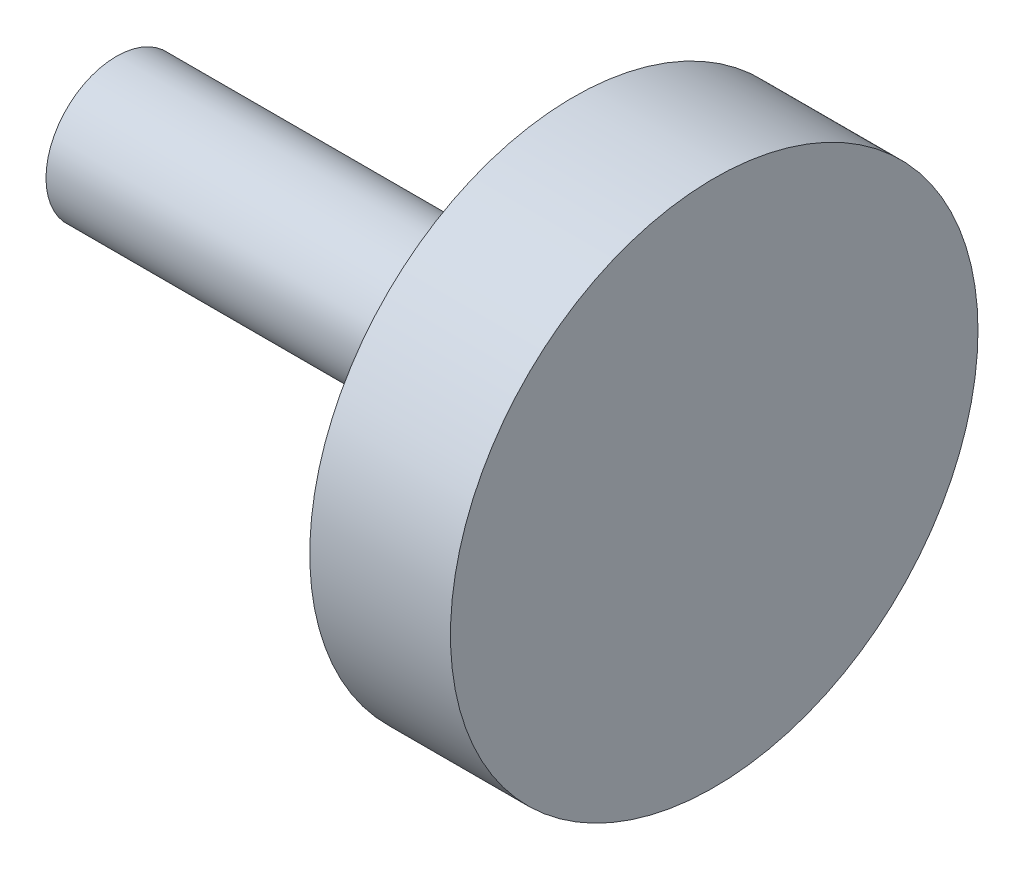
SolidWorks part; units mm, degrees
ref_plane "Front Plane" through (0, 0, 0) normal (0, 0, 1) x (1, 0, 0)
ref_plane "Top Plane" through (0, 0, 0) normal (0, 1, 0) x (1, 0, 0)
ref_plane "Right Plane" through (0, 0, 0) normal (1, 0, 0) x (0, 0, -1)
sketch "Sketch1" plane through (0, 0, 0) normal (1, 0, 0) x (0, 0, -1)
  circle A0 centre (0, 0) radius 7.5
  dimension "D1" = 15
extrude "Boss-Extrude1" add sketch "Sketch1" along normal blind 4
sketch "Sketch2" plane through (0, 0, 0) normal (-1, 0, 0) x (0, 0, 1)
  circle A0 centre (0, 0) radius 2
  dimension "D1" = 4
extrude "Boss-Extrude3" add sketch "Sketch2" along normal blind 13
